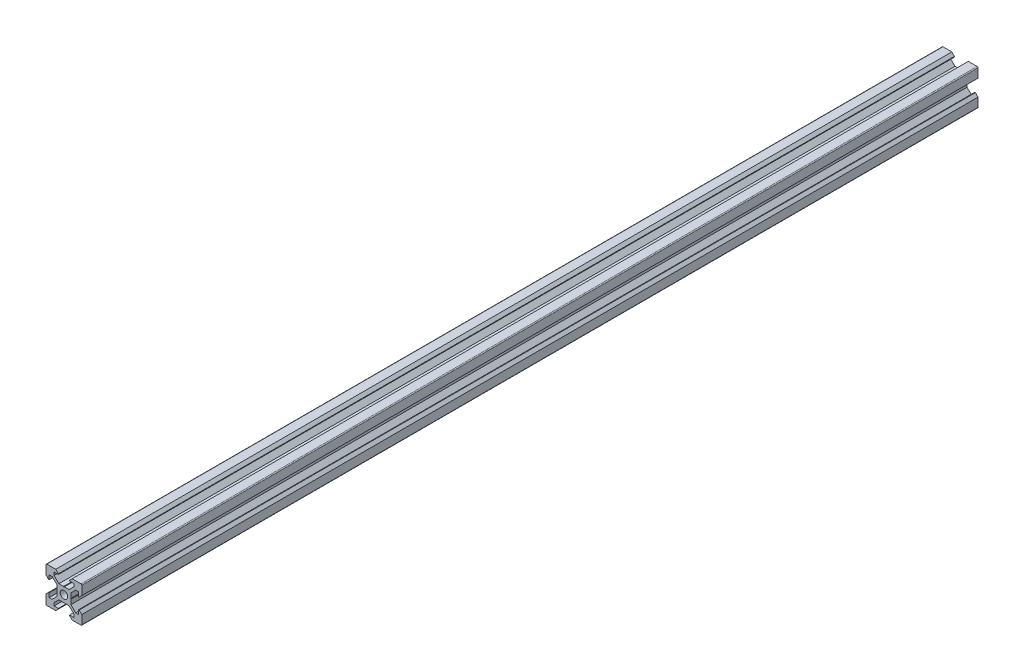
SolidWorks part; units mm, degrees
ref_plane "Front Plane" through (0, 0, 0) normal (0, 0, 1) x (1, 0, 0)
ref_plane "Top Plane" through (0, 0, 0) normal (0, 1, 0) x (1, 0, 0)
ref_plane "Right Plane" through (0, 0, 0) normal (1, 0, 0) x (0, 0, -1)
sketch "Sketch1" plane through (0, 0, 0) normal (0, 0, 1) x (1, 0, 0)
  line B0 (3.69, 0) -> (3.9, -0.21)
  line B1 (3.9, -0.21) -> (3.9, -2.8393)
  line B2 (3.9, -2.8393) -> (6.5607, -5.5)
  line B3 (6.5607, -5.5) -> (8.2, -5.5)
  line B4 (8.2, -5.5) -> (8.2, -3.125)
  line B5 (8.2, -3.125) -> (8.545, -3.125)
  line B6 (8.545, -3.125) -> (10, -4.58)
  line B7 (10, -9.5) -> (10, -4.58)
  arc B8 (9.5, -10) -> (10, -9.5) centre (9.5, -9.5) ccw
  line B9 (9.5, -10) -> (4.58, -10)
  line B10 (3.125, -8.545) -> (4.58, -10)
  line B11 (3.125, -8.2) -> (3.125, -8.545)
  line B12 (5.5, -8.2) -> (3.125, -8.2)
  line B13 (5.5, -6.5607) -> (5.5, -8.2)
  line B14 (2.8393, -3.9) -> (5.5, -6.5607)
  line B15 (0.21, -3.9) -> (2.8393, -3.9)
  line B16 (0, -3.69) -> (0.21, -3.9)
  line B17 (0, -3.69) -> (-0.21, -3.9)
  line B18 (-0.21, -3.9) -> (-2.8393, -3.9)
  line B19 (-2.8393, -3.9) -> (-5.5, -6.5607)
  line B20 (-5.5, -6.5607) -> (-5.5, -8.2)
  line B21 (-5.5, -8.2) -> (-3.125, -8.2)
  line B22 (-3.125, -8.2) -> (-3.125, -8.545)
  line B23 (-3.125, -8.545) -> (-4.58, -10)
  line B24 (-4.58, -10) -> (-9.5, -10)
  arc B25 (-10, -9.5) -> (-9.5, -10) centre (-9.5, -9.5) ccw
  line B26 (-10, -9.5) -> (-10, -4.58)
  line B27 (-8.545, -3.125) -> (-10, -4.58)
  line B28 (-8.2, -3.125) -> (-8.545, -3.125)
  line B29 (-8.2, -5.5) -> (-8.2, -3.125)
  line B30 (-6.5607, -5.5) -> (-8.2, -5.5)
  line B31 (-3.9, -2.8393) -> (-6.5607, -5.5)
  line B32 (-3.9, -0.21) -> (-3.9, -2.8393)
  line B33 (-3.69, 0) -> (-3.9, -0.21)
  line B34 (-3.69, 0) -> (-3.9, 0.21)
  line B35 (-3.9, 0.21) -> (-3.9, 2.8393)
  line B36 (-3.9, 2.8393) -> (-6.5607, 5.5)
  line B37 (-6.5607, 5.5) -> (-8.2, 5.5)
  line B38 (-8.2, 5.5) -> (-8.2, 3.125)
  line B39 (-8.2, 3.125) -> (-8.545, 3.125)
  line B40 (-8.545, 3.125) -> (-10, 4.58)
  line B41 (-10, 4.58) -> (-10, 9.5)
  arc B42 (-9.5, 10) -> (-10, 9.5) centre (-9.5, 9.5) ccw
  line B43 (-4.58, 10) -> (-9.5, 10)
  line B44 (-3.125, 8.545) -> (-4.58, 10)
  line B45 (-3.125, 8.2) -> (-3.125, 8.545)
  line B46 (-5.5, 8.2) -> (-3.125, 8.2)
  line B47 (-5.5, 6.5607) -> (-5.5, 8.2)
  line B48 (-2.8393, 3.9) -> (-5.5, 6.5607)
  line B49 (-0.21, 3.9) -> (-2.8393, 3.9)
  line B50 (0, 3.69) -> (-0.21, 3.9)
  line B51 (0, 3.69) -> (0.21, 3.9)
  line B52 (0.21, 3.9) -> (2.8393, 3.9)
  line B53 (2.8393, 3.9) -> (5.5, 6.5607)
  line B54 (5.5, 6.5607) -> (5.5, 8.2)
  line B55 (5.5, 8.2) -> (3.125, 8.2)
  line B56 (3.125, 8.2) -> (3.125, 8.545)
  line B57 (3.125, 8.545) -> (4.58, 10)
  line B58 (9.5, 10) -> (4.58, 10)
  arc B59 (10, 9.5) -> (9.5, 10) centre (9.5, 9.5) ccw
  line B60 (10, 4.58) -> (10, 9.5)
  line B61 (8.545, 3.125) -> (10, 4.58)
  line B62 (8.2, 3.125) -> (8.545, 3.125)
  line B63 (8.2, 5.5) -> (8.2, 3.125)
  line B64 (6.5607, 5.5) -> (8.2, 5.5)
  line B65 (3.9, 2.8393) -> (6.5607, 5.5)
  line B66 (3.9, 0.21) -> (3.9, 2.8393)
  line B67 (3.69, 0) -> (3.9, 0.21)
  circle B68 centre (0, 0) radius 2.1
sketch_block_instance "2020 - V-Slot-1"
sketch_block "2020 - V-Slot"
extrude "Boss-Extrude1" add sketch "Sketch1" along normal blind 500
